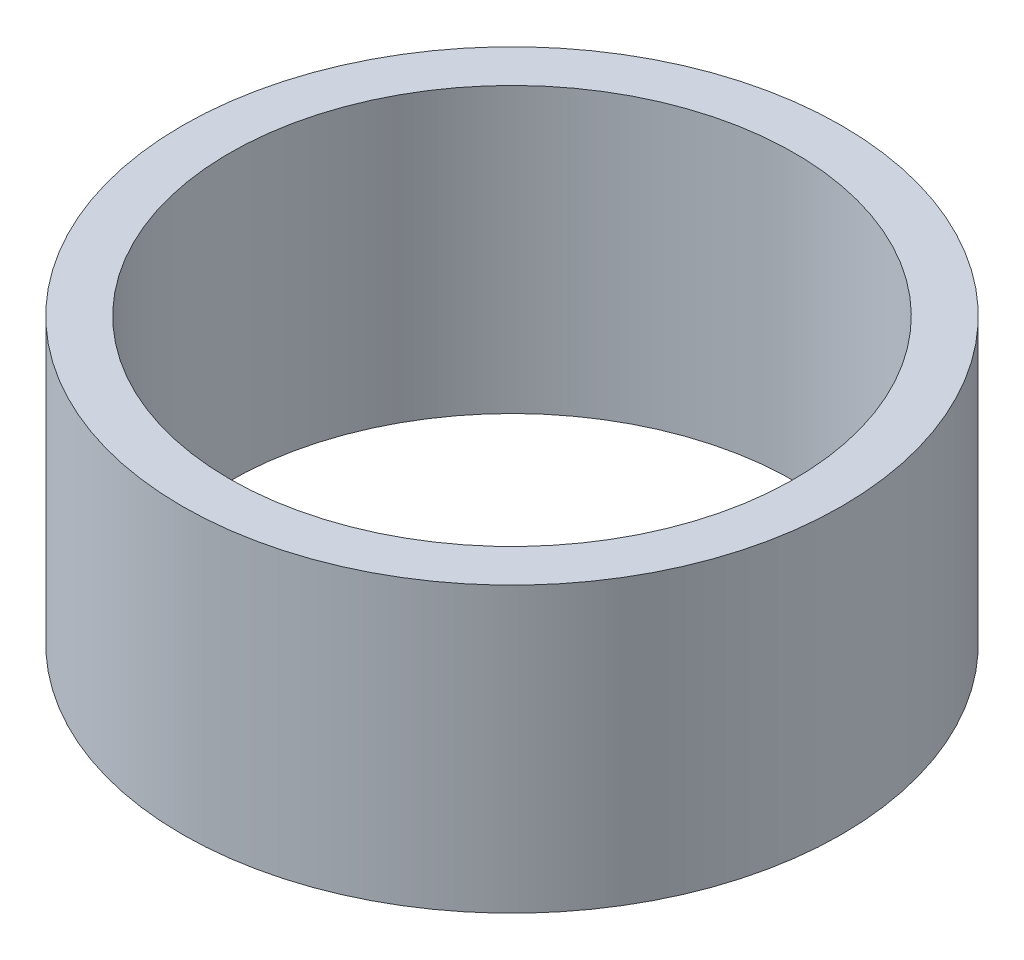
SolidWorks part; units mm, degrees
material "6061-T6 (SS)"
ref_plane "Front Plane" through (0, 0, 0) normal (0, 0, 1) x (1, 0, 0)
ref_plane "Top Plane" through (0, 0, 0) normal (0, 1, 0) x (1, 0, 0)
ref_plane "Right Plane" through (0, 0, 0) normal (1, 0, 0) x (0, 0, -1)
sketch "Sketch1" plane through (0, 0, 0) normal (0, 1, 0) x (1, 0, 0)
  circle A0 centre (0, 0) radius 13.925
  circle A1 centre (0, 0) radius 11.925
  dimension "D1" = 27.85
  dimension "D2" = 23.85
extrude "Boss-Extrude1" add sketch "Sketch1" along normal blind 12
equation "\"D2@Sketch1\"=\"D1@Sketch1\"-4"
